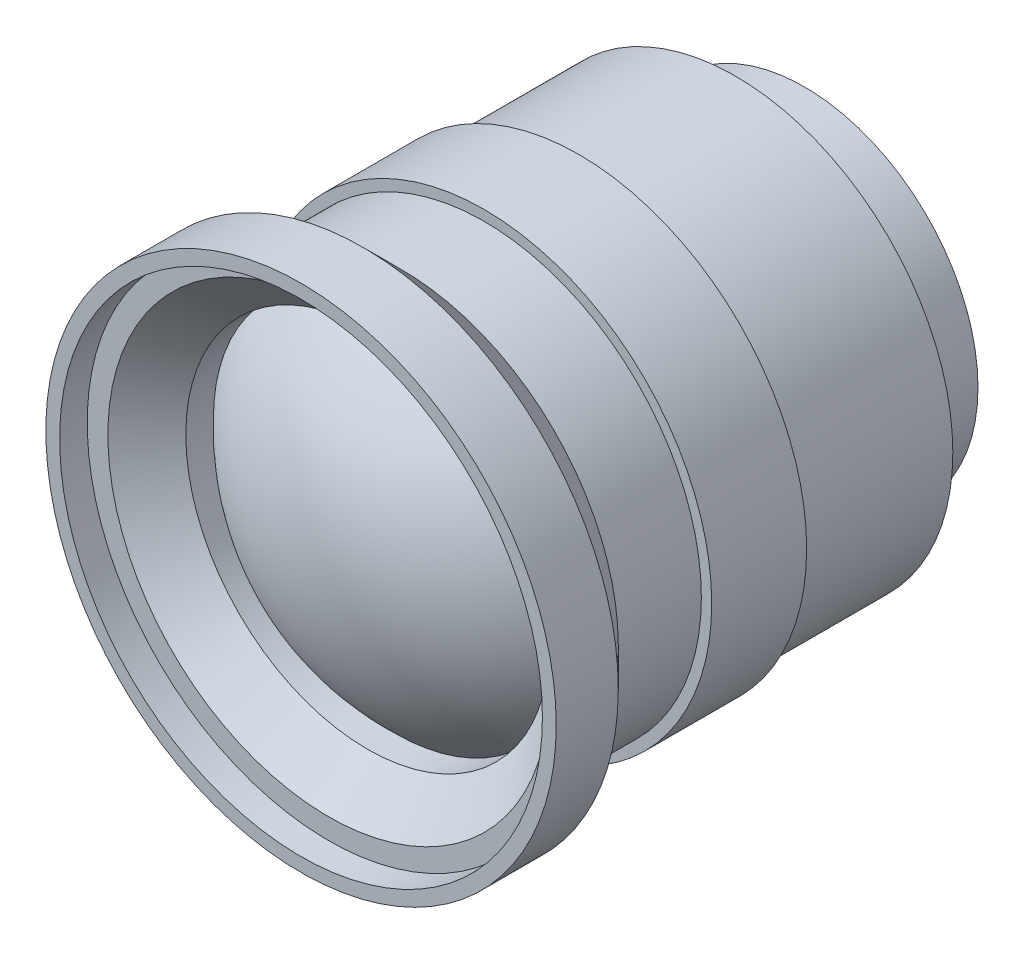
SolidWorks part; units mm, degrees
material "Tamron 22HA"
ref_plane "Front Plane" through (0, 0, 0) normal (0, 0, 1) x (1, 0, 0)
ref_plane "Top Plane" through (0, 0, 0) normal (0, 1, 0) x (1, 0, 0)
ref_plane "Right Plane" through (0, 0, 0) normal (1, 0, 0) x (0, 0, -1)
sketch "Sketch1" plane through (0, 0, 0) normal (1, 0, 0) x (0, 0, -1)
  line L0 (0, 0) -> (0, 12.575)
  line L1 (0, 12.575) -> (-5, 12.575)
  line L2 (-5, 12.575) -> (-5, 15.75)
  line L3 (-5, 15.75) -> (-16.3454, 15.75)
  line L4 (-16.3454, 15.75) -> (-16.3454, 16.5)
  line L5 (-16.3454, 16.5) -> (-23.2288, 16.5)
  line L6 (-23.2288, 16.5) -> (-23.2288, 15.75)
  line L7 (-23.2288, 15.75) -> (-29.2517, 15.75)
  line L8 (-29.2517, 15.75) -> (-32.0017, 18.5)
  line L9 (-32.0017, 18.5) -> (-36.5, 18.5)
  line L10 (-36.5, 18.5) -> (-36.5, 17.5)
  line L11 (-35.4614, 0) -> (0, 0)
  line L12 (-36.5, 17.5) -> (-34.5, 17.5)
  line L13 (-34.5, 17.5) -> (-34.5, 16)
  line L14 (-34.5, 16) -> (-31.676, 13.176)
  line L15 (-31.676, 13.176) -> (-29.676, 13.176)
  line L16 (-35.4614, 0) -> (-35.4614, 10.5303) construction
  arc A0 (-29.676, 13.176) -> (-35.4614, 0) centre (-17.5646, 0) ccw
  dimension "D1" = 5
  dimension "D2" = 31.5
  dimension "D3" = 18.5
  dimension "D4" = 15.75
  dimension "D5" = 16.5
  dimension "D6" = 135
  dimension "D7" = 12.575
  dimension "D8" = 1
  dimension "D9" = 1.5
  dimension "D10" = 2
  dimension "D11" = 2
revolve "Revolve1" add sketch "Sketch1" angle 360 about L11
